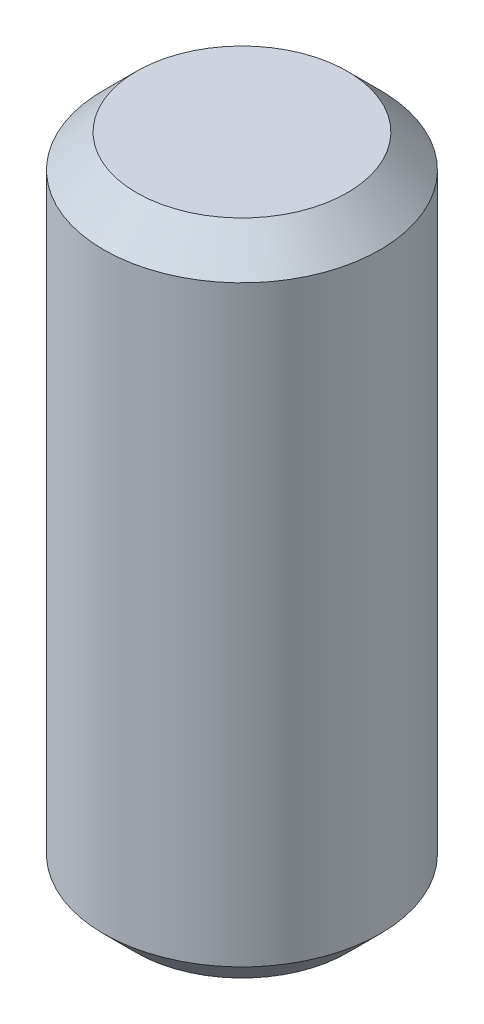
SolidWorks part; units mm, degrees
material "6061-T6 (SS)"
ref_plane "Płaszczyzna przednia" through (0, 0, 0) normal (0, 0, 1) x (1, 0, 0)
ref_plane "Płaszczyzna górna" through (0, 0, 0) normal (0, 1, 0) x (1, 0, 0)
ref_plane "Płaszczyzna prawa" through (0, 0, 0) normal (1, 0, 0) x (0, 0, -1)
sketch "Szkic1" plane through (0, 0, 0) normal (0, 1, 0) x (1, 0, 0)
  circle A0 centre (0, 0) radius 42
  dimension "D1" = 84
extrude "Dodanie-wyciągnięcie1" add sketch "Szkic1" along normal blind 200
chamfer "Sfazowanie1" distance 10 angle 45 2 edges at (0, 0, 42) (0, 200, 42)
shell "Skorupa1" thickness 0.2
sketch "Szkic8" plane through (0, 200, 0) normal (0, 1, 0) x (1, 0, 0)
  circle A3 centre (0, 0) radius 32 construction
  circle A4 centre (0, 0) radius 32
extrude "Dodanie-wyciągnięcie4" add sketch "Szkic8" against normal blind 0.2
